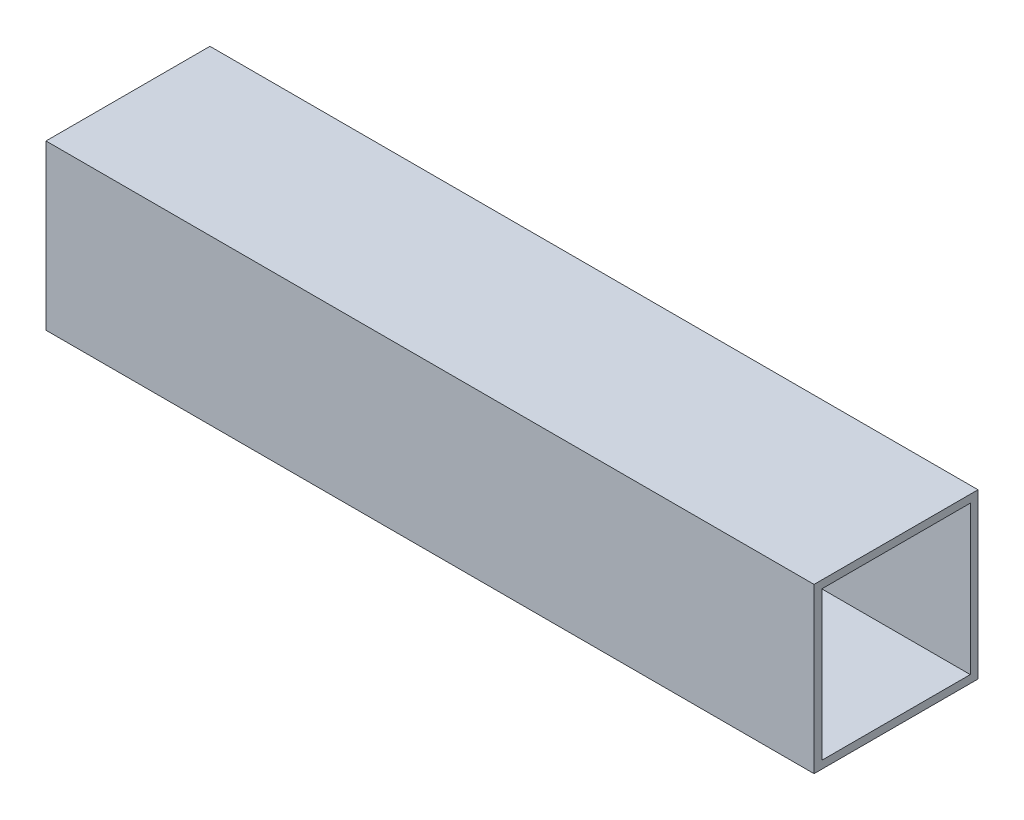
SolidWorks part; units mm, degrees
ref_plane "Alzado" through (0, 0, 0) normal (0, 0, 1) x (1, 0, 0)
ref_plane "Planta" through (0, 0, 0) normal (0, 1, 0) x (1, 0, 0)
ref_plane "Vista lateral" through (0, 0, 0) normal (1, 0, 0) x (0, 0, -1)
sketch "Sketch1" plane through (0, 0, 0) normal (0, 1, 0) x (1, 0, 0)
  line L0 (0, 0) -> (119, 0)
  line L1 (119, 0) -> (119, 25.4)
  line L2 (119, 25.4) -> (0, 25.4)
  line L3 (0, 25.4) -> (0, 0)
  dimension "D1" = 119
  dimension "D2" = 25.4
extrude "Boss-Extrude1" add sketch "Sketch1" along normal blind 25.4
sketch "Sketch2" plane through (119, 0, 0) normal (1, 0, 0) x (0, 0, -1)
  line L0 (1.2, 24.2) -> (24.2, 24.2)
  line L1 (24.2, 24.2) -> (24.2, 1.2)
  line L2 (1.2, 24.2) -> (1.2, 1.2)
  line L3 (1.2, 1.2) -> (24.2, 1.2)
  line L4 (0, 25.4) -> (0, 0) construction
  line L5 (0, 25.4) -> (25.4, 25.4) construction
  line L6 (25.4, 25.4) -> (25.4, 0) construction
  line L7 (0, 0) -> (25.4, 0) construction
  dimension "D1" = 1.2
  dimension "D2" = 1.2
  dimension "D3" = 1.2
  dimension "D4" = 1.2
extrude "Cut-Extrude1" cut sketch "Sketch2" against normal blind 450
